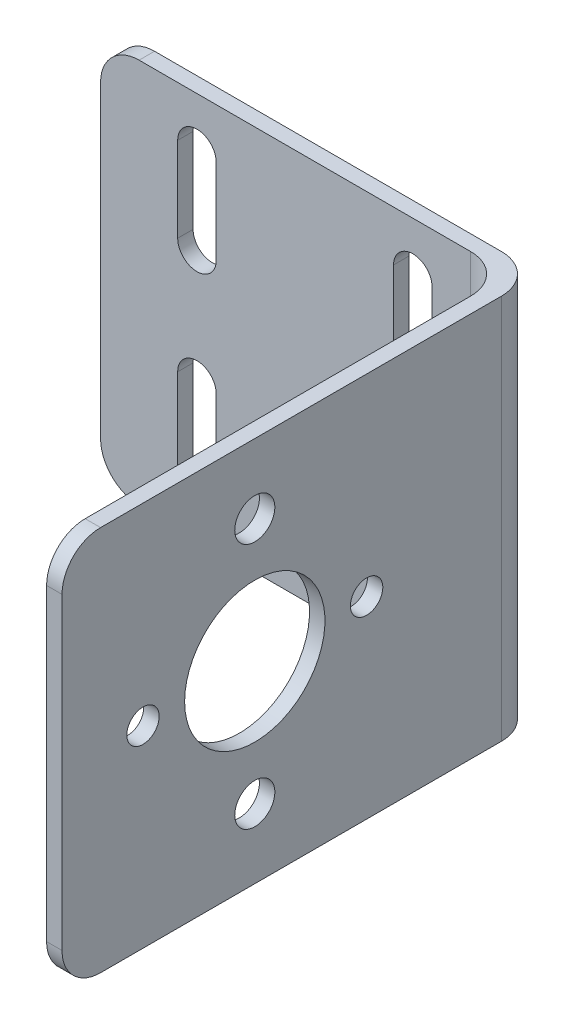
SolidWorks part; units mm, degrees
ref_plane "Front Plane" through (0, 0, 0) normal (1, 0, 0) x (0, 1, 0)
ref_plane "Top Plane" through (0, 0, 0) normal (0, 0, 1) x (0, 1, 0)
ref_plane "Right Plane" through (0, 0, 0) normal (0, 1, 0) x (-1, 0, 0)
sketch "Sketch1" plane through (0, 0, 0) normal (0, 0, 1) x (0, 1, 0)
  line L1 (-25, 26.5) -> (25, 26.5)
  line L2 (-25, 26.5) -> (-25, -26.5)
  line L3 (-25, -26.5) -> (25, -26.5)
  line L4 (25, 26.5) -> (25, -26.5)
  line L5 (-25, 26.5) -> (25, -26.5) construction
  line L6 (-25, -26.5) -> (25, 26.5) construction
  point P0 (0, 0)
  dimension "D1" = 50
  dimension "D2" = 53
extrude "Boss-Extrude1" add sketch "Sketch1" along normal blind 2
sketch "Sketch2" plane through (0, 0, 0) normal (0, 0, 1) x (0, 1, 0)
  line L1 (-25, -26.5) -> (25, -26.5)
  line L2 (-25, -26.5) -> (-25, -28.5)
  line L3 (-25, -28.5) -> (25, -28.5)
  line L4 (25, -26.5) -> (25, -28.5)
  dimension "D1" = 50
  dimension "D2" = 2
extrude "Boss-Extrude2" add sketch "Sketch2" along normal blind 62
sketch "Sketch3" plane through (26.5, 0, 0) normal (-1, 0, 0) x (0, -1, 0)
  line L0 (-25, 2) -> (25, 2) construction
  circle A0 centre (0, 37) radius 9.1
  circle A1 centre (16, 37) radius 2.6
  circle A2 centre (-16, 37) radius 2.6
  circle A3 centre (0, 51.5) radius 2.1
  circle A4 centre (0, 22.5) radius 2.1
  dimension "D2" = 18.2
  dimension "D3" = 5.2
  dimension "D4" = 5.2
  dimension "D7" = 4.2
  dimension "D8" = 4.2
  dimension "D1" = 35
  dimension "D5" = 16
  dimension "D6" = 16
  dimension "D9" = 14.5
  dimension "D10" = 14.5
extrude "Cut-Extrude1" cut sketch "Sketch3" against normal up to surface (2 mm away) up to face at (28.5, 0, 31)
sketch "Sketch4" plane through (0, 0, 2) normal (0, 0, 1) x (1, 0, 0)
  line L0 (-14, 18.5) -> (-14, 7.5) construction
  line L1 (-11.5, 18.5) -> (-11.5, 7.5)
  line L2 (-16.5, 18.5) -> (-16.5, 7.5)
  line L3 (-14, -7.5) -> (-14, -18.5) construction
  line L4 (-11.5, -7.5) -> (-11.5, -18.5)
  line L5 (-16.5, -7.5) -> (-16.5, -18.5)
  line L6 (14, 18.5) -> (14, 7.5) construction
  line L7 (16.5, 18.5) -> (16.5, 7.5)
  line L8 (11.5, 18.5) -> (11.5, 7.5)
  line L9 (14, -7.5) -> (14, -18.5) construction
  line L10 (16.5, -7.5) -> (16.5, -18.5)
  line L11 (11.5, -7.5) -> (11.5, -18.5)
  line L12 (-26.5, 25) -> (-26.5, -25) construction
  line L13 (26.5, 25) -> (-26.5, 25) construction
  line L14 (-26.5, -25) -> (26.5, -25) construction
  line L15 (26.5, -25) -> (26.5, 25) construction
  arc A0 (-11.5, 18.5) -> (-16.5, 18.5) centre (-14, 18.5) ccw
  arc A1 (-16.5, 7.5) -> (-11.5, 7.5) centre (-14, 7.5) ccw
  arc A2 (-11.5, -7.5) -> (-16.5, -7.5) centre (-14, -7.5) ccw
  arc A3 (-16.5, -18.5) -> (-11.5, -18.5) centre (-14, -18.5) ccw
  arc A4 (16.5, 18.5) -> (11.5, 18.5) centre (14, 18.5) ccw
  arc A5 (11.5, 7.5) -> (16.5, 7.5) centre (14, 7.5) ccw
  arc A6 (16.5, -7.5) -> (11.5, -7.5) centre (14, -7.5) ccw
  arc A7 (11.5, -18.5) -> (16.5, -18.5) centre (14, -18.5) ccw
  point P2 (-14, 13)
  point P9 (-14, -13)
  point P16 (14, 13)
  point P23 (14, -13)
  point P30 (-14, 21)
  point P34 (-14, -21)
  point P37 (14, -21)
  point P40 (14, 21)
  dimension "D2" = 2.5
  dimension "D7" = 2.5
  dimension "D10" = 2.5
  dimension "D12" = 2.5
  dimension "D1" = 11
  dimension "D3" = 10
  dimension "D4" = 4
  dimension "D5" = 10
  dimension "D6" = 11
  dimension "D8" = 4
  dimension "D9" = 11
  dimension "D11" = 11
  dimension "D13" = 4
  dimension "D14" = 10
  dimension "D15" = 10
  dimension "D16" = 4
extrude "Cut-Extrude2" cut sketch "Sketch4" against normal up to surface (2 mm away) up to face at (1, 0, 0)
fillet "Fillet1" radius 5 6 edges at (-26.5, -25, 1) (-26.5, 25, 1) (26.5, 0, 2) (28.5, 0, 0) (27.5, -25, 62) (27.5, 25, 62)
